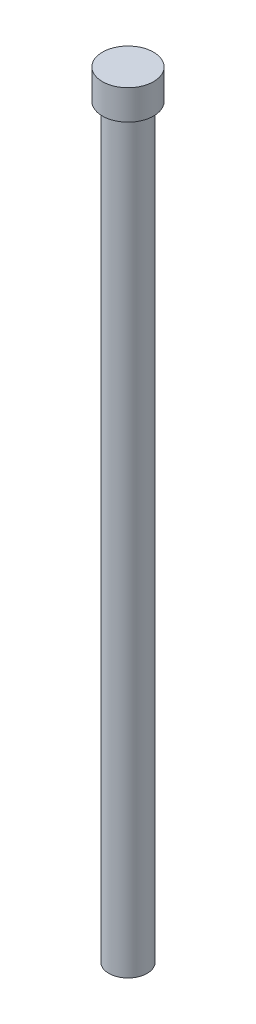
SolidWorks part; units mm, degrees
ref_plane "Front Plane" through (0, 0, 0) normal (0, 0, 1) x (1, 0, 0)
ref_plane "Top Plane" through (0, 0, 0) normal (0, 1, 0) x (1, 0, 0)
ref_plane "Right Plane" through (0, 0, 0) normal (1, 0, 0) x (0, 0, -1)
sketch "Sketch1" plane through (0, 0, 0) normal (0, 1, 0) x (1, 0, 0)
  circle A0 centre (0, 0) radius 0.9
  dimension "D1" = 1.8
extrude "nail_shaft_body" add sketch "Sketch1" along normal blind 35
sketch "Sketch2" plane through (0, 35, 0) normal (0, 1, 0) x (1, 0, 0)
  circle A0 centre (0, 0) radius 1.2
  dimension "D1" = 2.4
extrude "nail_head" add sketch "Sketch2" along normal blind 1.4
